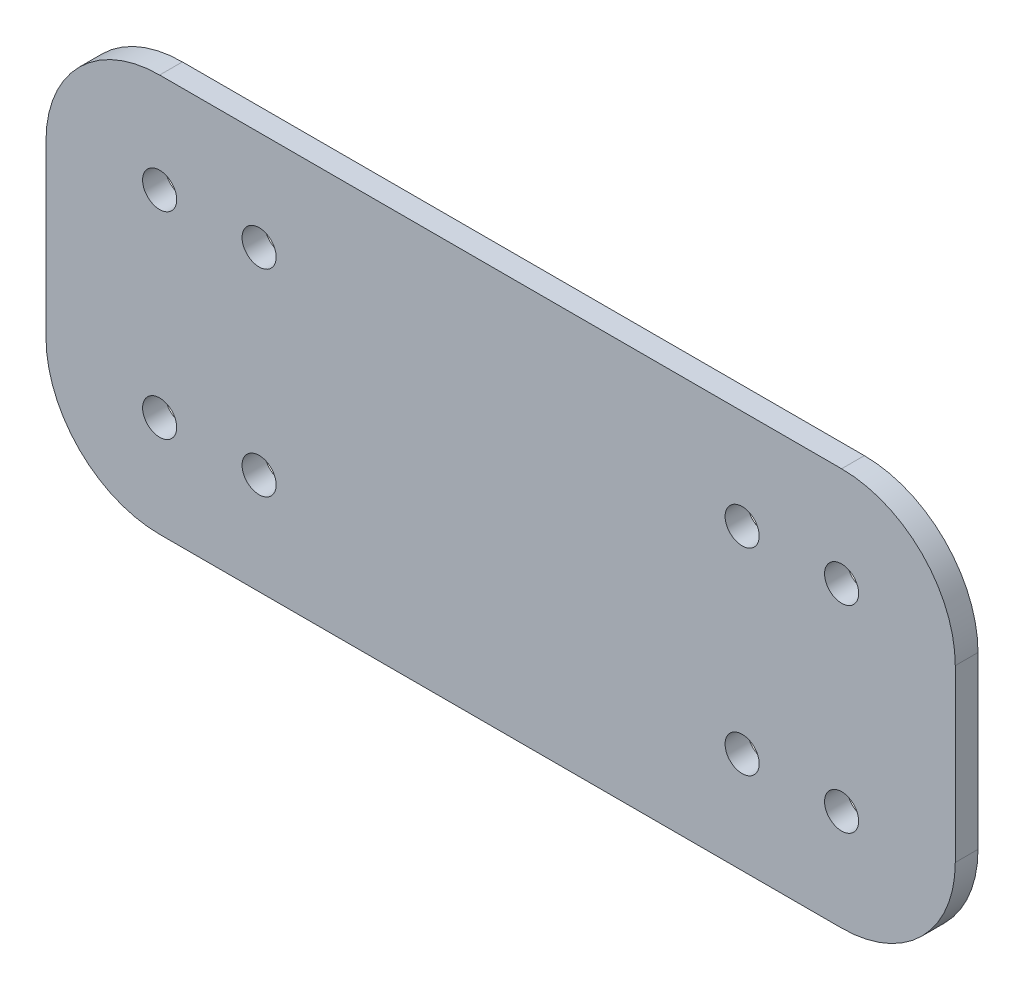
SolidWorks part; units mm, degrees
ref_plane "前视基准面" through (0, 0, 0) normal (0, 0, 1) x (1, 0, 0)
ref_plane "上视基准面" through (0, 0, 0) normal (0, 1, 0) x (1, 0, 0)
ref_plane "右视基准面" through (0, 0, 0) normal (1, 0, 0) x (0, 0, -1)
other "Configuration Table"
sketch "草图2" plane through (0, 0, 0) normal (0, 0, 1) x (1, 0, 0)
  line L0 (-50.3604, 22.3704) -> (9.6396, 22.3704)
  line L1 (19.6396, 12.3704) -> (19.6396, -2.6296)
  line L2 (9.6396, -12.6296) -> (-50.3604, -12.6296)
  line L3 (-60.3604, -2.6296) -> (-60.3604, 12.3704)
  arc A0 (19.6396, -2.6296) -> (9.6396, -12.6296) centre (9.6396, -2.6296) cw
  arc A1 (9.6396, 22.3704) -> (19.6396, 12.3704) centre (9.6396, 12.3704) cw
  arc A2 (-50.3604, -12.6296) -> (-60.3604, -2.6296) centre (-50.3604, -2.6296) cw
  arc A3 (-50.3604, 22.3704) -> (-60.3604, 12.3704) centre (-50.3604, 12.3704) ccw
  dimension "D1" = 10
  dimension "D2" = 80
  dimension "D3" = 15
extrude "凸台-拉伸1" add sketch "草图2" along normal blind 2
sketch "草图3" plane through (0, 0, 0) normal (0, 0, -1) x (-1, 0, 0)
  line L1 (20.3604, 22.3704) -> (20.3604, -12.6296)
  line L3 (-9.6396, 22.3704) -> (50.3604, 22.3704) construction
  line L9 (50.3604, -12.6296) -> (-9.6396, -12.6296) construction
  point P0 (50.3604, 13.6204)
  point P1 (50.3604, -3.7322)
  point P4 (41.6104, 13.6204)
  point P8 (41.6104, -3.7322)
  point P12 (-0.8896, -3.7322)
  point P13 (-9.6396, -3.7322)
  point P15 (-9.6396, 13.6204)
  point P16 (-0.8896, 13.6204)
  dimension "D1" = 8.75
  dimension "D2" = 17.3526
hole_wizard "大小mm 暗销孔2" positions "3D草图4" profile "草图7" hole size "Ø3.0" standard "GB" end condition through all
sketch3d "3D草图4"
  point P0 (-41.6104, 13.6204, 0)
  point P3 (-50.3604, 13.6204, 0)
  point P6 (-41.6104, -3.7322, 0)
  point P9 (-50.3604, -3.7322, 0)
sketch "草图7" plane through (-41.6104, 13.6204, 0) normal (1, 0, 0) x (0, 1, 0)
  line L0 (0, 0) -> (0, 2)
  line L1 (0, 2) -> (1.5, 2)
  line L2 (1.5, 2) -> (1.5, 0)
  line L5 (1.5, 0) -> (0, 0)
  line L11 (0, -6.35) -> (0, 107.95) construction
  dimension "通孔孔直径" = 3
  dimension "通孔孔深度" = 2
sketch3d "3D草图5" plane through (0, 0, 0) normal (0, 0, 1) x (1, 0, 0)
hole_wizard "大小mm 暗销孔3" positions "3D草图6" profile "草图8" hole size "Ø3.0" standard "GB" end condition through all
sketch3d "3D草图6"
  point P0 (9.6396, 13.6204, 0)
  point P3 (0.8896, 13.6204, 0)
  point P6 (0.8896, -3.7322, 0)
  point P9 (9.6396, -3.7322, 0)
sketch "草图8" plane through (9.6396, 13.6204, 0) normal (1, 0, 0) x (0, 1, 0)
  line L0 (0, 0) -> (0, 2)
  line L1 (0, 2) -> (1.5, 2)
  line L2 (1.5, 2) -> (1.5, 0)
  line L5 (1.5, 0) -> (0, 0)
  line L11 (0, -6.35) -> (0, 107.95) construction
  dimension "通孔孔直径" = 3
  dimension "通孔孔深度" = 2
